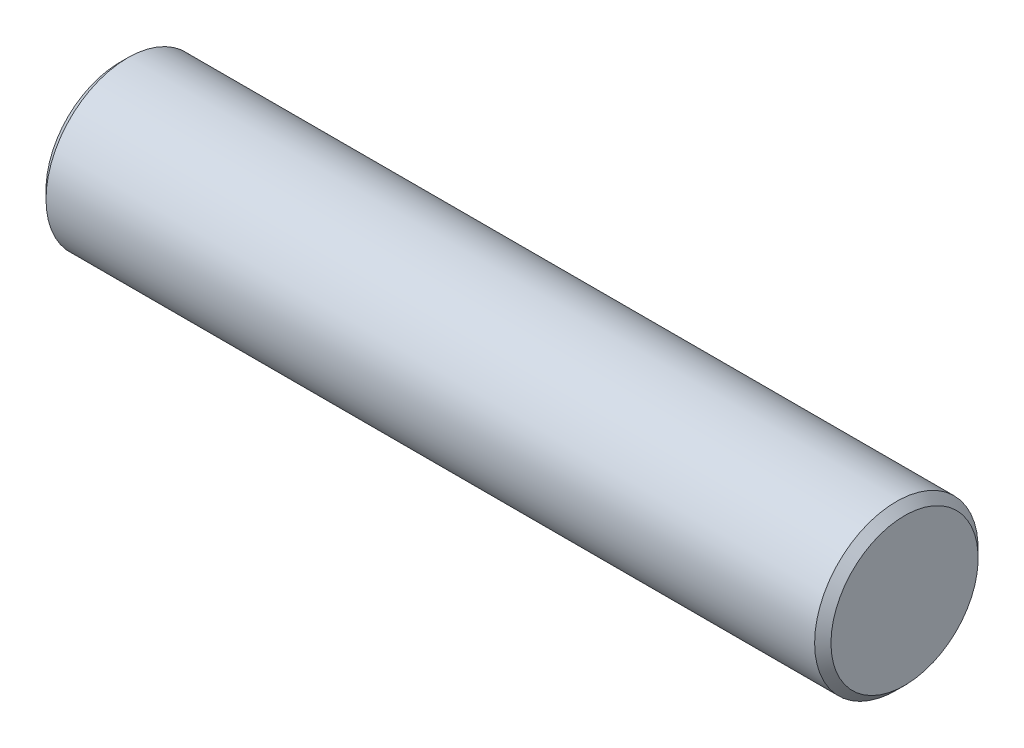
SolidWorks part; units mm, degrees
ref_plane "Спереди" through (0, 0, 0) normal (0, 0, 1) x (1, 0, 0)
ref_plane "Сверху" through (0, 0, 0) normal (0, 1, 0) x (1, 0, 0)
ref_plane "Справа" through (0, 0, 0) normal (1, 0, 0) x (0, 0, -1)
sketch "Эскиз1" plane through (0, 0, 0) normal (0, 0, 1) x (1, 0, 0)
  line L0 (0, 0) -> (14.3069, 0) construction
  line L1 (0, 0) -> (0, 6.3046) construction
  line L3 (0, 2.5) -> (24, 2.5)
  line L6 (24, 2.5) -> (24, -0.4836) construction
  line L7 (-0.75, 0) -> (24.75, 0) construction
  line L8 (24, 2.5) -> (24, 0)
  line L9 (24, 0) -> (0, 0)
  line L10 (0, 0) -> (0, 2.5)
  dimension "D2" = 5
  dimension "D3" = 24
revolve "Повернуть2" add sketch "Эскиз1" angle 360 about L0
chamfer "Фаска1" distance 0.25 angle 45 2 edges at (0, 0, 2.5) (24, 0, 2.5)
